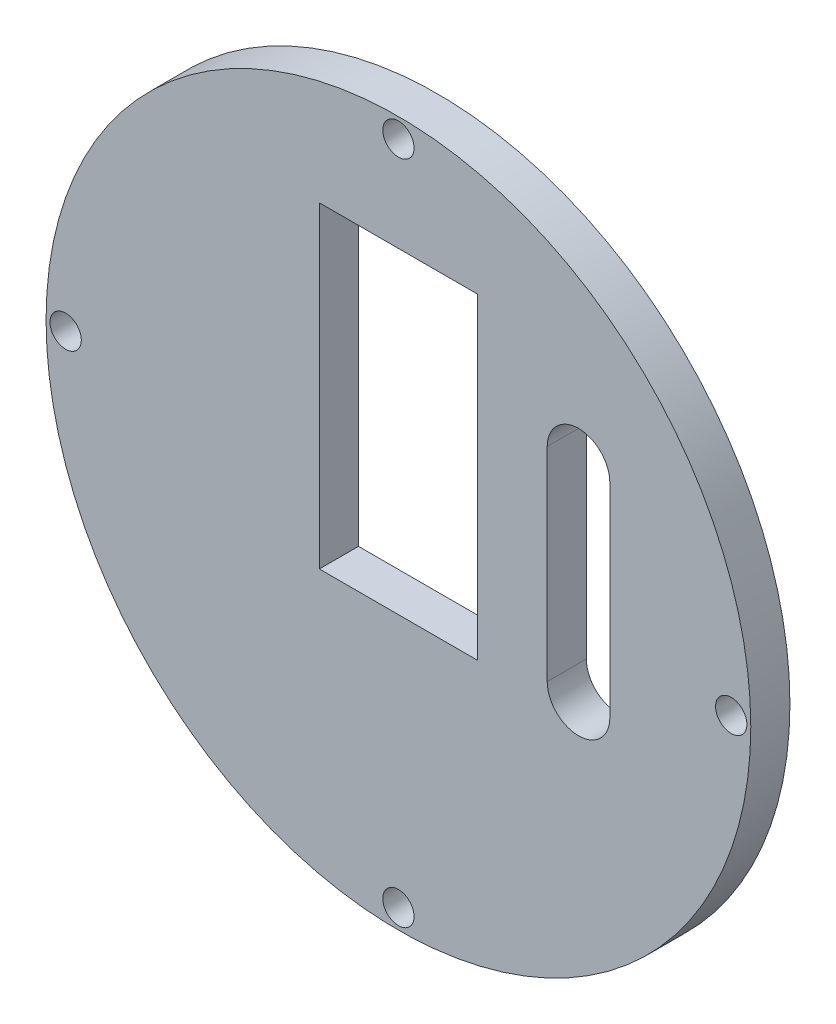
SolidWorks part; units mm, degrees
ref_plane "Front Plane" through (0, 0, 0) normal (0, 0, 1) x (1, 0, 0)
ref_plane "Top Plane" through (0, 0, 0) normal (0, 1, 0) x (1, 0, 0)
ref_plane "Right Plane" through (0, 0, 0) normal (1, 0, 0) x (0, 0, -1)
sketch "Sketch1" plane through (0, 0, 0) normal (0, 0, 1) x (1, 0, 0)
  line L0 (0, 61.1562) -> (0, -62.0155) construction
  line L1 (-10.1, 30.4) -> (10.1, 30.4)
  line L2 (-10.1, 30.4) -> (-10.1, -10.1)
  line L3 (-10.1, -10.1) -> (10.1, -10.1)
  line L4 (10.1, 30.4) -> (10.1, -10.1)
  line L5 (-10.1, 30.4) -> (10.1, -10.1) construction
  line L6 (-10.1, -10.1) -> (10.1, 30.4) construction
  line L7 (-62.9195, 0) -> (73.7046, 0) construction
  circle A0 centre (0, 0) radius 45
  circle A1 centre (0, 0) radius 1.25 construction
  circle A6 centre (42.5, 0) radius 2
  circle A7 centre (0, -42.5) radius 2
  circle A8 centre (-42.5, 0) radius 2
  circle A9 centre (0, 42.5) radius 2
  circle A10 centre (0, 0) radius 42.5 construction
  point P2 (0, 10.15)
  point P11 (5, -92.894)
  point P12 (5, 90.4881)
  point P13 (-96.2355, -5)
  point P14 (94.097, -5)
  point P15 (-5, -92.894)
  point P16 (-5, 90.4881)
  point P17 (-96.2355, 5)
  point P18 (94.097, 5)
  point P35 (0, 0)
  dimension "D1" = 90
  dimension "D5" = 2.5
  dimension "D14" = 4
  dimension "D13" = 85
  dimension "D2" = 20.2
  dimension "D3" = 40.5
  dimension "D15" = 4
  dimension "D4" = 10.1
extrude "Boss-Extrude1" add sketch "Sketch1" along normal blind 5
sketch "Sketch2" plane through (0, 0, 0) normal (0, 0, -1) x (-1, 0, 0)
  line L0 (-23, 18) -> (-23, -8) construction
  line L1 (-19, 18) -> (-19, -8)
  line L2 (-27, 18) -> (-27, -8)
  line L3 (10.1, 30.4) -> (-10.1, 30.4) construction
  arc A0 (-19, 18) -> (-27, 18) centre (-23, 18) ccw
  arc A1 (-27, -8) -> (-19, -8) centre (-23, -8) ccw
  point P2 (-23, 5)
  dimension "D1" = 4
  dimension "D5" = 18
  dimension "D2" = 20.2
  dimension "D3" = 23
  dimension "D4" = 5
extrude "Cut-Extrude1" cut sketch "Sketch2" against normal blind 10
